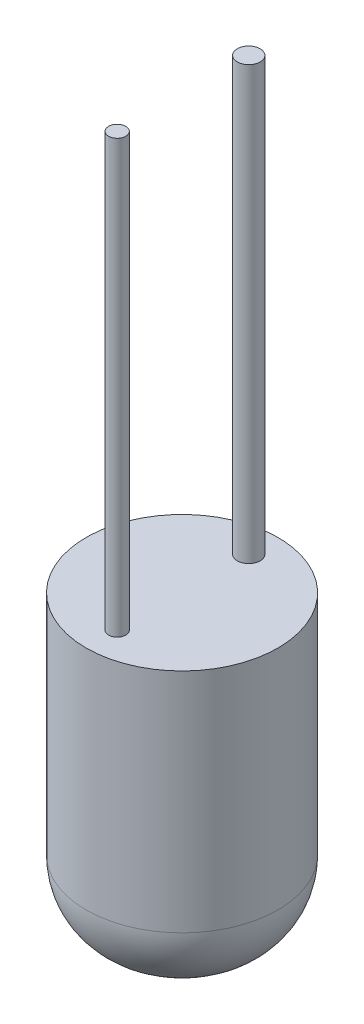
SolidWorks part; units mm, degrees
ref_plane "Front Plane" through (0, 0, 0) normal (0, 0, 1) x (1, 0, 0)
ref_plane "Top Plane" through (0, 0, 0) normal (0, 1, 0) x (1, 0, 0)
ref_plane "Right Plane" through (0, 0, 0) normal (1, 0, 0) x (0, 0, -1)
sketch "Sketch1" plane through (0, 0, 0) normal (0, 1, 0) x (1, 0, 0)
  circle A0 centre (0, 0) radius 2.2543
extrude "Boss-Extrude1" add sketch "Sketch1" along normal blind 7.112
sketch "Sketch2" plane through (0, 7.112, 0) normal (0, 1, 0) x (1, 0, 0)
  circle A1 centre (0, 1.5679) radius 0.2688
  circle A2 centre (0, -1.5249) radius 0.2022
extrude "Boss-Extrude2" add sketch "Sketch2" along normal blind 10.16
fillet "Fillet4" radius 1.778 1 edges at (0, 0, 2.2543)
